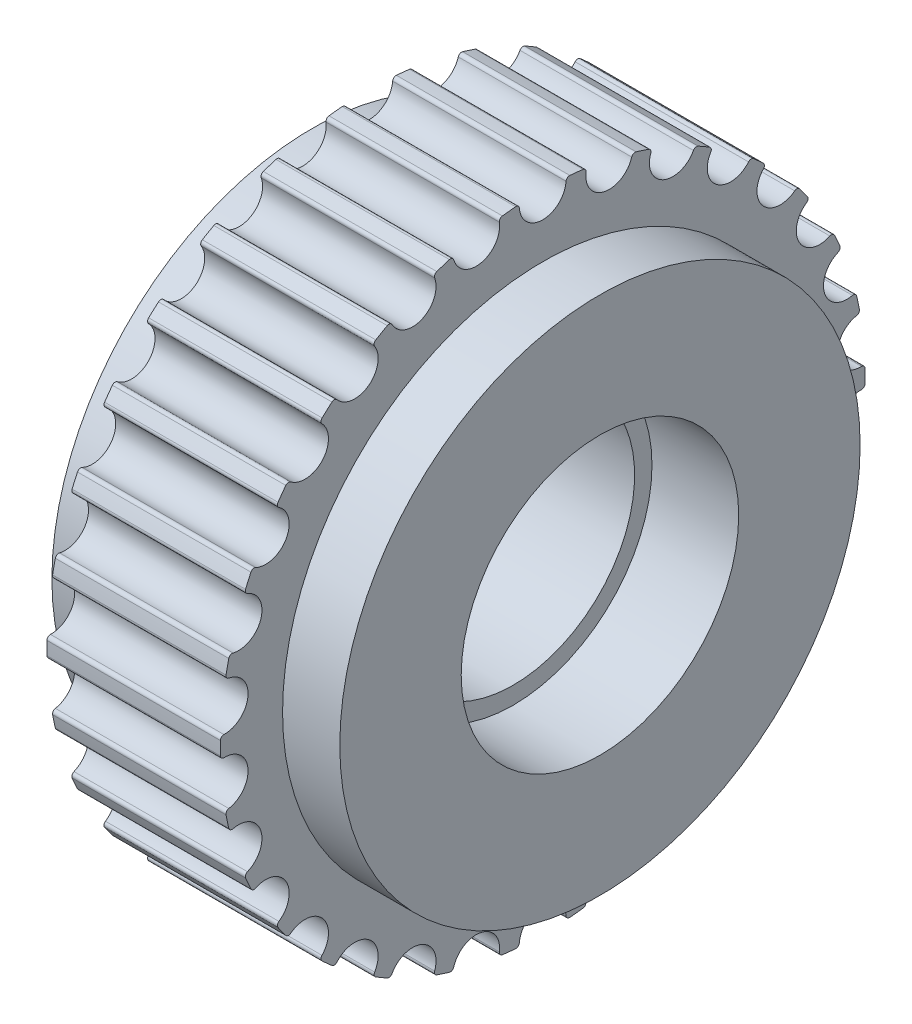
SolidWorks part; units mm, degrees
ref_plane "Front Plane" through (0, 0, 0) normal (0, 0, 1) x (1, 0, 0)
ref_plane "Top Plane" through (0, 0, 0) normal (0, 1, 0) x (1, 0, 0)
ref_plane "Right Plane" through (0, 0, 0) normal (1, 0, 0) x (0, 0, -1)
sketch "Sketch1" plane through (0, 0, 0) normal (0, 0, 1) x (1, 0, 0)
  line L0 (0, 0) -> (8.3, 0) construction
  line L1 (0, 4) -> (2.5, 4)
  line L2 (2.5, 4) -> (2.5, 3.5)
  line L3 (2.5, 3.5) -> (5.8, 3.5)
  line L4 (5.8, 3.5) -> (5.8, 4)
  line L5 (5.8, 4) -> (8.3, 4)
  line L6 (8.3, 4) -> (8.3, 7.5)
  line L7 (8.3, 7.5) -> (6.65, 7.5)
  line L8 (6.65, 7.5) -> (6.65, 9.295)
  line L9 (6.65, 9.295) -> (1.65, 9.295)
  line L10 (1.65, 9.295) -> (1.65, 7.5)
  line L11 (1.65, 7.5) -> (0, 7.5)
  line L12 (0, 7.5) -> (0, 4)
  line L13 (1.65, 9.55) -> (6.65, 9.55) construction
  line L14 (0, 2.5) -> (8.3, 2.5) construction
  dimension "W" = 8.3
  dimension "A" = 5
  dimension "Dh" = 7
  dimension "D" = 8
  dimension "E" = 15
  dimension "O.D." = 18.59
  dimension "P.D." = 19.1
  dimension "D_s" = 5
revolve "Revolve1" add sketch "Sketch1" angle 360 about L0
sketch "Sketch2" [suppressed] plane through (2.2, 0, 0) normal (1, 0, 0) x (0, 0, -1)
  line L0 (0, 0) -> (0, 21.71) construction
  line L2 (-0.7244, 19.8868) -> (-1.66, 21.6464)
  line L3 (0.7244, 19.8868) -> (1.66, 21.6464)
  circle A1 centre (0, 0) radius 21.71 construction
  circle A3 centre (0, 0) radius 19.9 construction
  circle A4 centre (0, 0) radius 22.281 construction
  arc A9 (-1.66, 21.6464) -> (1.66, 21.6464) centre (0, 0) cw
  arc A10 (-0.7244, 19.8868) -> (0.7244, 19.8868) centre (0, 0) cw
  dimension "MSM_6" = 3.32
  dimension "MSM_7" = 28
  dimension "MSM_1" = 0.75
  dimension "MSM_2" = 0.254
extrude "Cut-Extrude1" [suppressed] cut sketch "Sketch2" along normal through all
fillet "Fillet1" [suppressed] radius 0.2
fillet "Fillet2" [suppressed] radius 0.2
pattern_circular "CirPattern1" [suppressed] count 30 over 360
sketch "Sketch3" plane through (0, 0, 0) normal (-1, 0, 0) x (0, 0, 1)
  line L0 (0, 0) -> (0, 9.22) construction
  circle A0 centre (0, 0) radius 8.545 construction
  circle A1 centre (0, 0) radius 9.549 construction
  circle A2 centre (0, 0) radius 9.295 construction
  arc A3 (-0.6731, 9.2706) -> (0.6731, 9.2706) centre (0, 9.22) ccw
  arc A8 (-0.6731, 9.2706) -> (0.6731, 9.2706) centre (0, 0) cw
  dimension "O.D." = 18.59
  dimension "MSM_10" = 0.675
  dimension "MSM_1" = 0.75
  dimension "MSM_2" = 0.254
extrude "Cut-Extrude2" cut sketch "Sketch3" against normal through all
fillet "Fillet3" radius 0.1 2 edges at (4.15, 9.2706, -0.6731) (4.15, 9.2706, 0.6731)
pattern_circular "CirPattern2" count 30 over 360 about axis through (0, 0, 0) along (1, 0, 0) of "Cut-Extrude2", "Fillet3"
